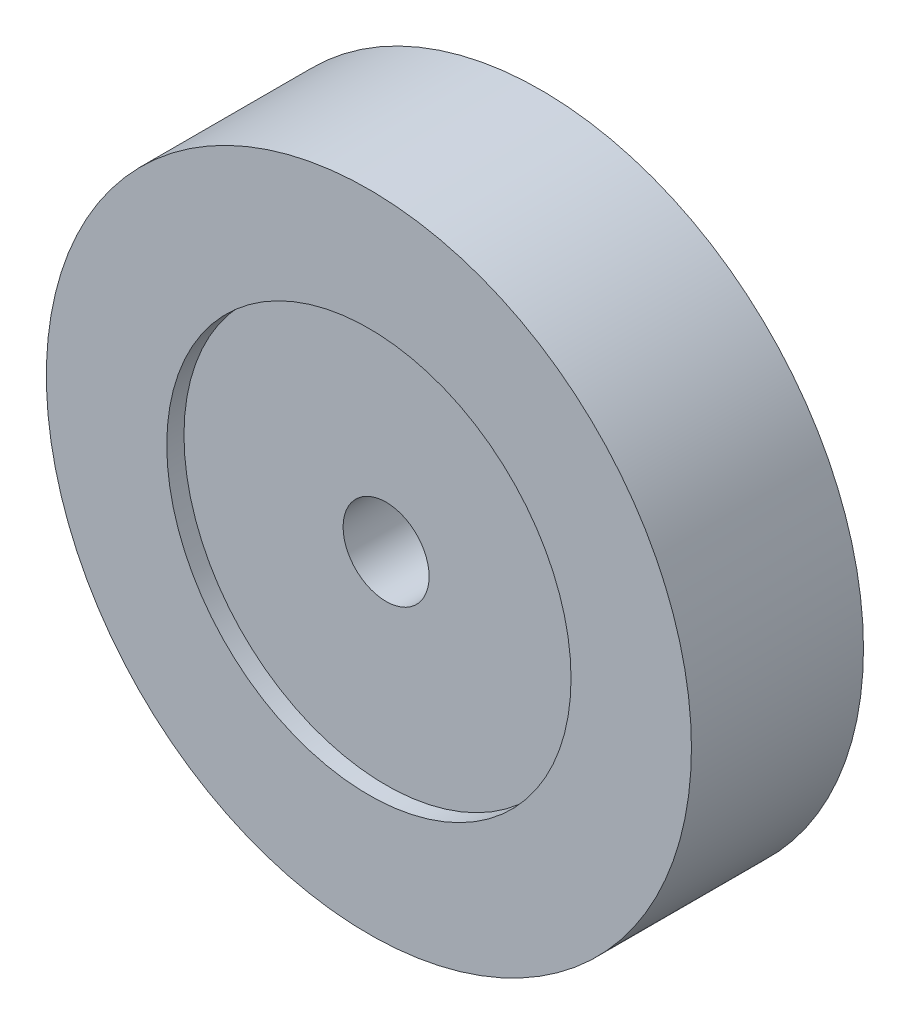
SolidWorks part; units mm, degrees
ref_plane "Front Plane" through (0, 0, 0) normal (0, 0, 1) x (1, 0, 0)
ref_plane "Top Plane" through (0, 0, 0) normal (0, 1, 0) x (1, 0, 0)
ref_plane "Right Plane" through (0, 0, 0) normal (1, 0, 0) x (0, 0, -1)
sketch "Sketch1" plane through (0, 0, 0) normal (0, 0, 1) x (1, 0, 0)
  circle A0 centre (0, 0) radius 4.7625
  circle A1 centre (0, 0) radius 0.635
  dimension "D1" = 9.525
  dimension "D2" = 1.27
extrude "Boss-Extrude1" add sketch "Sketch1" along normal blind 2.54
sketch "Sketch2" plane through (0, 0, 2.54) normal (0, 0, 1) x (1, 0, 0)
  circle A0 centre (0, 0) radius 2.9845
  dimension "D1" = 5.969
extrude "Cut-Extrude1" cut sketch "Sketch2" against normal blind 0.254 contours A0
sketch "Sketch3" plane through (0, 0, 0) normal (0, 0, -1) x (-1, 0, 0)
  circle A0 centre (0, 0) radius 2.9845
  dimension "D1" = 5.969
extrude "Cut-Extrude2" cut sketch "Sketch3" against normal blind 0.254
